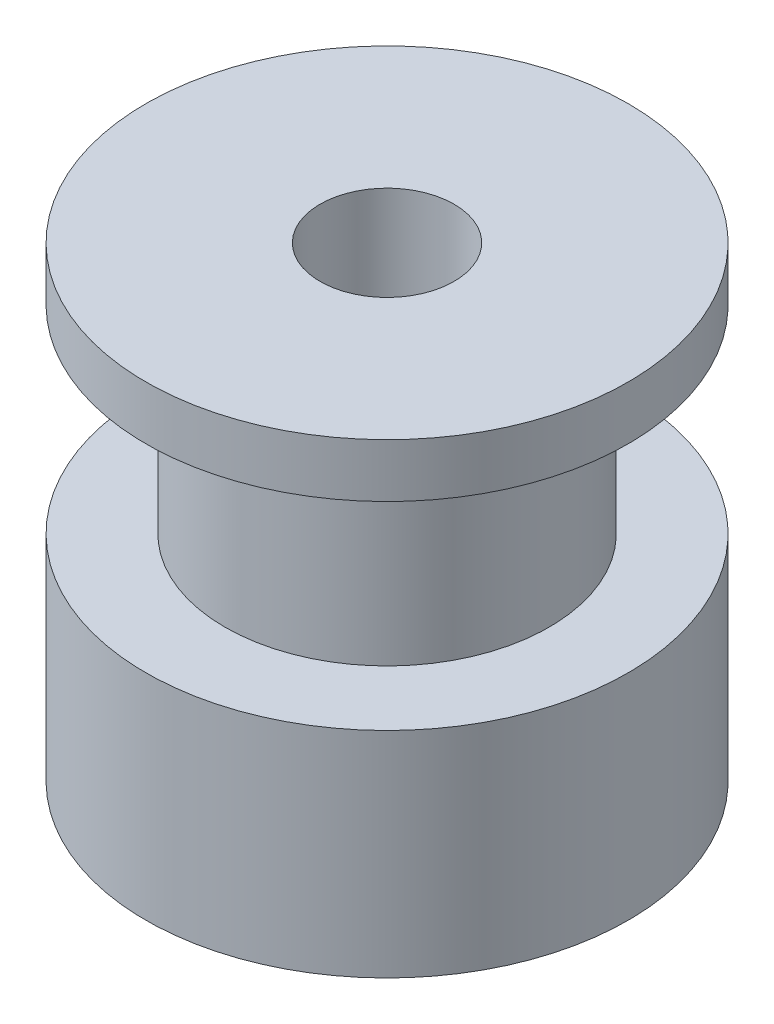
SolidWorks part; units mm, degrees
ref_plane "Спереди" through (0, 0, 0) normal (0, 0, 1) x (1, 0, 0)
ref_plane "Сверху" through (0, 0, 0) normal (0, 1, 0) x (1, 0, 0)
ref_plane "Справа" through (0, 0, 0) normal (1, 0, 0) x (0, 0, -1)
sketch "Эскиз1" plane through (0, 0, 0) normal (0, 0, 1) x (1, 0, 0)
  line L0 (0, 0) -> (0, 17.4) construction
  line L1 (-2.5, 17.4) -> (-9, 17.4)
  line L2 (-9, 17.4) -> (-9, 15.4)
  line L3 (-9, 15.4) -> (-6.05, 15.4)
  line L4 (-6.05, 15.4) -> (-6.05, 8)
  line L5 (-6.05, 8) -> (-9, 8)
  line L6 (-9, 8) -> (-9, 0)
  line L7 (-9, 0) -> (-2.5, 0)
  line L8 (-2.5, 17.4) -> (-2.5, 0)
  line L9 (-2.5, 17.4) -> (0, 17.4) construction
  line L10 (0, 0) -> (-2.5, 0) construction
  dimension "D1" = 18
  dimension "D2" = 7.4
  dimension "D3" = 2
  dimension "D4" = 8
  dimension "D5" = 5
  dimension "D6" = 12.1
revolve "Повернуть1" add sketch "Эскиз1" angle 360 about L0
